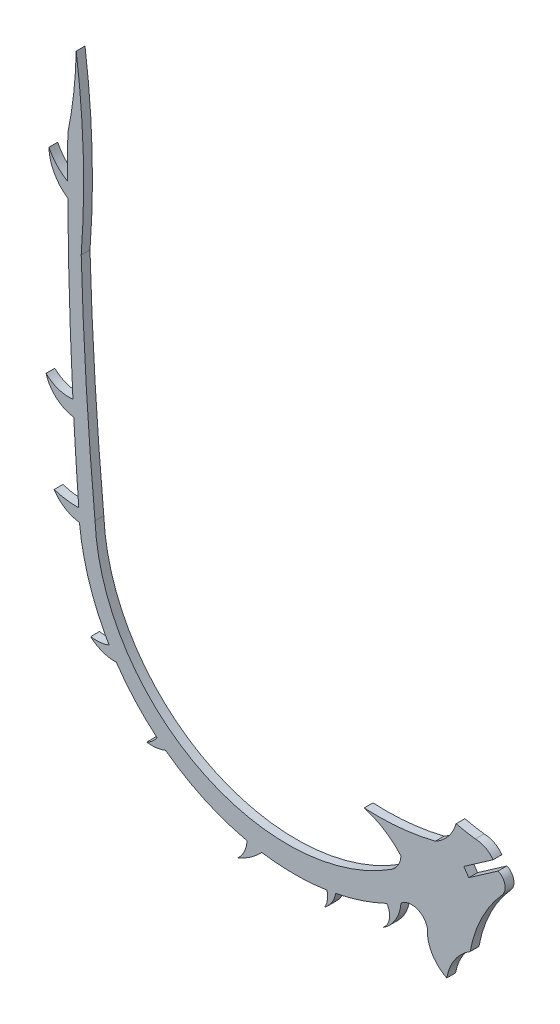
SolidWorks part; units mm, degrees
ref_plane "Front Plane" through (0, 0, 0) normal (0, 0, 1) x (1, 0, 0)
ref_plane "Top Plane" through (0, 0, 0) normal (0, 1, 0) x (1, 0, 0)
ref_plane "Right Plane" through (0, 0, 0) normal (1, 0, 0) x (0, 0, -1)
sketch "Sketch1" plane through (0, 0, 0) normal (0, 0, 1) x (1, 0, 0)
  line L0 (37.7043, -31.7057) -> (32.6217, -35.2455)
  line L1 (32.6217, -35.2455) -> (33.4939, -36.4982)
  line L2 (33.4939, -36.4982) -> (38.5766, -32.9575)
  arc A0 (39.316, -36.1534) -> (38.5766, -32.9575) centre (37.742, -34.8341) ccw
  arc A1 (39.316, -36.1534) -> (33.7362, -47.4069) centre (56.3709, -51.6197) ccw
  arc A2 (33.7367, -47.4663) -> (33.7362, -47.4069) centre (30.0201, -47.4663) ccw
  arc A3 (26.3093, -47.6771) -> (21.7404, -46.181) centre (23.5817, -48.2822) ccw
  arc A4 (-29.8064, -31.0321) -> (-28.8501, -32.7559) centre (3.252, -13.818) ccw
  arc A5 (-34.1921, -13.8136) -> (-34.1623, -14.7736) centre (4.6594, -13.0856) ccw
  arc A6 (-36.0306, 40.5493) -> (-36.0438, 33.2536) centre (625.2368, 35.6995) ccw
  arc A7 (-33.7038, 23.3954) -> (-31.308, -15.3099) centre (556.5915, 40.5064) ccw
  arc A8 (-31.308, -15.3099) -> (20.0642, -41.9665) centre (2.0862, -13.7834) ccw
  arc A9 (20.0642, -41.9665) -> (21.7232, -39.1004) centre (18.1289, -38.9331) ccw
  arc A10 (37.7043, -31.7057) -> (34.6169, -30.1162) centre (34.6169, -33.9093) ccw
  arc A11 (18.5414, -51.4772) -> (21.7404, -46.181) centre (14.8362, -45.6251) ccw
  arc A12 (18.5414, -51.4772) -> (19.2893, -47.463) centre (16.8024, -49.0764) ccw
  arc A13 (8.4789, -53.4498) -> (10.4372, -50.3906) centre (5.4577, -49.3595) ccw
  arc A14 (8.4789, -53.4498) -> (8.8921, -50.6605) centre (5.5018, -51.5836) ccw
  arc A15 (-6.5944, -53.5774) -> (-2.3997, -50.6588) centre (-11.4224, -42.165) ccw
  arc A16 (-6.5944, -53.5774) -> (-4.956, -50.1747) centre (-9.7595, -49.9576) ccw
  arc A17 (-22.3561, -44.0699) -> (-19.0673, -43.6682) centre (-21.4593, -37.7484) ccw
  arc A18 (-22.3561, -44.0699) -> (-20.5647, -42.4876) centre (-24.1708, -40.2103) ccw
  arc A19 (-32.065, -33.0797) -> (-27.6126, -34.712) centre (-27.8599, -28.498) ccw
  arc A20 (-32.065, -33.0797) -> (-28.8501, -32.7559) centre (-31.0696, -26.841) ccw
  arc A21 (-38.4025, -14.1638) -> (-34.0095, -16.9178) centre (-33.2831, -10.8784) ccw
  arc A22 (-38.4025, -14.1638) -> (-34.1623, -14.7736) centre (-34.3721, -1.1856) ccw
  arc A23 (-39.7958, 2.5881) -> (-34.9946, -1.6177) centre (-34.1301, 4.2126) ccw
  arc A24 (-39.7958, 2.5881) -> (-35.1391, 1.0333) centre (-35.8941, 6.5231) ccw
  arc A25 (-39.3063, 36.7708) -> (-36.0299, 30.7604) centre (-31.7509, 36.9911) ccw
  arc A26 (-39.3063, 36.7708) -> (-36.0438, 33.2536) centre (-31.7788, 40.4813) ccw
  arc A27 (10.4372, -50.3906) -> (19.2893, -47.463) centre (3.252, -13.818) ccw
  arc A28 (-2.3997, -50.6588) -> (8.8921, -50.6605) centre (3.252, -13.818) ccw
  arc A29 (-19.0673, -43.6682) -> (-4.956, -50.1747) centre (3.252, -13.818) ccw
  arc A30 (-27.6126, -34.712) -> (-20.5647, -42.4876) centre (3.252, -13.818) ccw
  arc A31 (-34.0095, -16.9178) -> (-29.8064, -31.0321) centre (4.6594, -13.0856) ccw
  arc A32 (-34.9946, -1.6177) -> (-34.1921, -13.8136) centre (625.2368, 35.6995) ccw
  arc A33 (-36.0299, 30.7604) -> (-35.1391, 1.0333) centre (625.2368, 35.6995) ccw
  arc A34 (15.3537, -35.0937) -> (27.7007, -33.9162) centre (17.6383, 6.2719) ccw
  arc A35 (21.7232, -39.1004) -> (15.3537, -35.0937) centre (11.7437, -47.8988) ccw
  arc A36 (-36.0306, 40.5493) -> (-34.572, 53.5774) centre (-106.1107, 54.9911) ccw
  arc A37 (-33.7038, 23.3954) -> (-34.572, 53.5774) centre (-176.6886, 34.3859) ccw
  arc A38 (27.7007, -33.9162) -> (31.2931, -29.4979) centre (24.2328, -27.427) ccw
  arc A39 (31.2931, -29.4979) -> (34.6169, -30.1162) centre (40.519, 10.8584) ccw
  arc A40 (33.7367, -47.4663) -> (29.679, -53.467) centre (38.3407, -54.9519) ccw
  arc A41 (26.3093, -47.6771) -> (29.679, -53.467) centre (32.324, -48.052) ccw
extrude "Boss-Extrude1" add sketch "Sketch1" along normal blind 1.524
